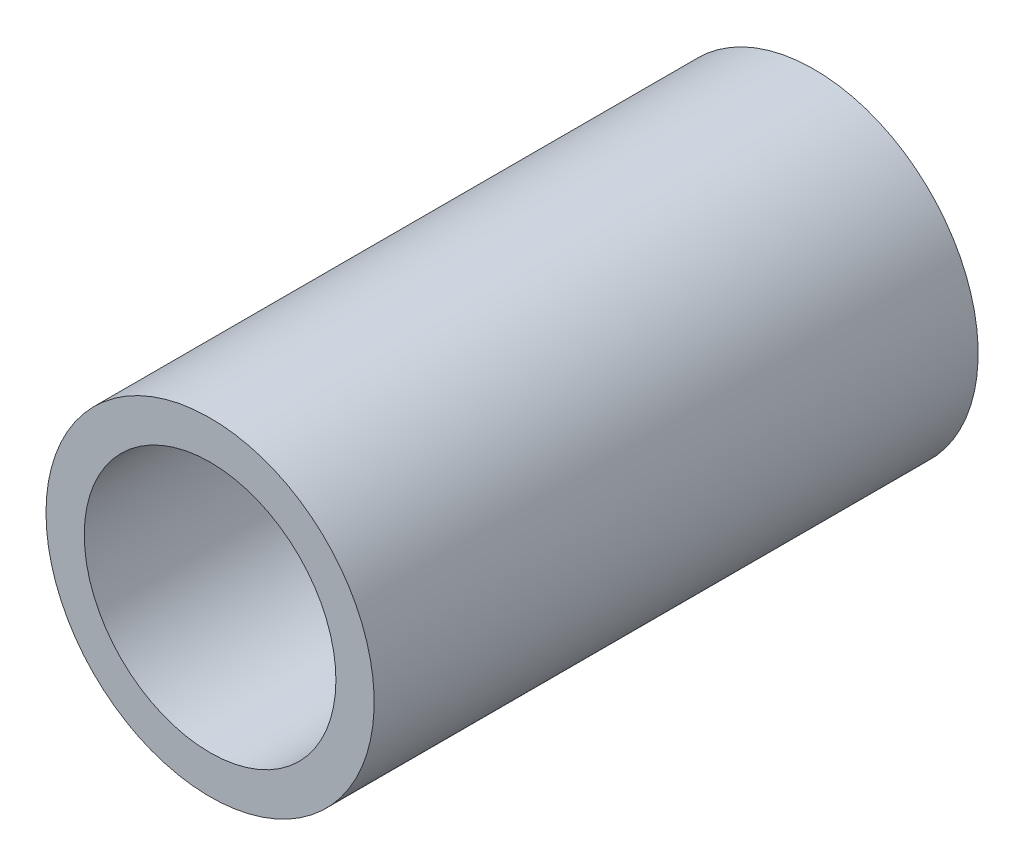
SolidWorks part; units mm, degrees
ref_plane "Front Plane" through (0, 0, 0) normal (0, 0, 1) x (1, 0, 0)
ref_plane "Top Plane" through (0, 0, 0) normal (0, 1, 0) x (1, 0, 0)
ref_plane "Right Plane" through (0, 0, 0) normal (1, 0, 0) x (0, 0, -1)
sketch "Sketch1" plane through (0, 0, 0) normal (0, 0, 1) x (1, 0, 0)
  circle A0 centre (0, 0) radius 10.3505
  circle A1 centre (0, 0) radius 7.9375
  dimension "OD" = 20.701
  dimension "ID" = 15.875
sketch "Sketch2" plane through (0, 0, 0) normal (1, 0, 0) x (0, 0, -1)
  line L2 (19.05, 0) -> (-19.05, 0) construction
  line L4 (-19.05, -10.3505) -> (-19.05, 10.3505) construction
  line L5 (-19.05, -7.9375) -> (19.05, -7.9375)
  line L6 (19.05, 7.9375) -> (-19.05, 7.9375)
  line L7 (19.05, -10.3505) -> (19.05, 10.3505) construction
  line L8 (-19.05, 10.3505) -> (19.05, 10.3505) construction
  line L9 (-19.05, -10.3505) -> (19.05, -10.3505) construction
  line L10 (0, 10.3505) -> (0, -10.3505) construction
  line L11 (0, 7.9375) -> (0, -7.9375) construction
  point P4 (0, -7.9375)
  point P7 (0, 7.9375)
  point P8 (0, 0)
  point P12 (-19.05, 0)
  point P15 (19.05, 0)
  point P16 (0, -10.3505)
  point P17 (0, 10.3505)
  dimension "Length" = 38.1
sketch "Sketch5" plane through (0, 0, 0) normal (0, 0, 1) x (1, 0, 0)
  circle A1 centre (0, 0) radius 7.9375
  circle A2 centre (0, 0) radius 7.9375
  circle A3 centre (0, 0) radius 10.3505
  circle A4 centre (0, 0) radius 10.3505
  dimension "D1" = 0
  dimension "D2" = 0
extrude "Boss-Extrude1" add sketch "Sketch5" along normal mid plane 38.1
equation "\"D1@Boss-Extrude1\" = \"Length@Sketch2\""
